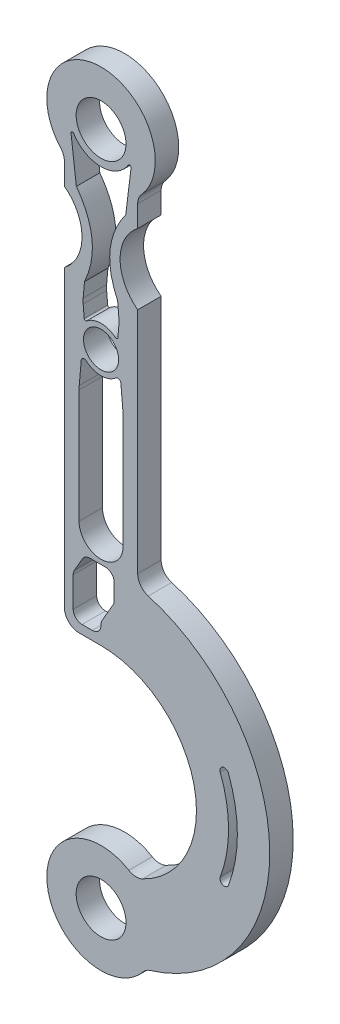
SolidWorks part; units mm, degrees
material "1.0577 (S355J2G4)"
ref_plane "Front Plane" through (0, 0, 0) normal (0, 0, 1) x (1, 0, 0)
ref_plane "Top Plane" through (0, 0, 0) normal (0, 1, 0) x (1, 0, 0)
ref_plane "Right Plane" through (0, 0, 0) normal (1, 0, 0) x (0, 0, -1)
sketch "Sketch1" plane through (0, 0, 0) normal (0, 0, 1) x (1, 0, 0)
  line L0 (-12.5, -13.6382) -> (-12.5, -23)
  line L1 (12.5, -13.6382) -> (12.5, -23)
  line L2 (0, 0) -> (0, -87.0636) construction
  line L3 (-12.5, -47) -> (-12.5, -154.9531)
  line L4 (12.5, -47) -> (12.5, -128.8307)
  line L5 (0, -152.4567) -> (-12.5, -152.4567)
  line L6 (15.2393, -240.4887) -> (11.4444, -215.4646) construction
  line L7 (0, -230) -> (17.3612, -226.5161)
  line L8 (-12.5, -13) -> (12.5, -13) construction
  line L9 (12.5, -57) -> (-12.5, -57) construction
  line L10 (15.3984, 118.8193) -> (165.3984, 118.8193) construction
  line L11 (-7.5, -119.4567) -> (-7.5, -80.6549)
  line L12 (6.7563, -71.4995) -> (7.4429, -79.3476)
  line L13 (-6.7563, -71.4995) -> (-7.4429, -79.3476)
  line L14 (7.5, -119.4567) -> (7.5, -80.6549)
  line L15 (-10.2431, -6.1641) -> (-8.4215, -21)
  line L16 (10.2431, -6.1641) -> (8.4215, -21)
  line L17 (-11, 0) -> (-10.6733, -2.6611) construction
  line L18 (11, 0) -> (10.6733, -2.6611) construction
  line L19 (0, -65) -> (24.057, -65) construction
  line L20 (6.5501, -60.8577) -> (7.4429, -50.6524) construction
  line L21 (-6.5501, -60.8577) -> (-7.4429, -50.6524) construction
  line L22 (-5.7376, -58.6709) -> (-6.0948, -54.5877)
  line L23 (-6.1711, -53.7161) -> (-17.293, -53.7161) construction
  line L24 (5.7376, -58.6709) -> (6.0948, -54.5877)
  line L25 (5.6481, -47.739) -> (6.0948, -52.8446)
  line L26 (-5.6481, -47.739) -> (-6.0948, -52.8446)
  line L27 (35.2514, 318.7905) -> (255.9181, 318.7905) construction
  line L28 (-9.5, -47) -> (-9.5, -154.9531) construction
  line L29 (0, -149.4567) -> (-12.5, -149.4567) construction
  line L30 (-3, -149.4567) -> (-6.5, -149.4567)
  line L31 (-9.5, -146.4567) -> (-9.5, -136.2605)
  line L32 (-9.0981, -134.7605) -> (-6.366, -130.0285)
  line L33 (-3.7679, -128.5285) -> (1.5, -128.5285)
  line L34 (4.5, -131.5285) -> (4.5, -136.8586)
  line L35 (4.0981, -138.3586) -> (0.4019, -144.7605)
  line L36 (0, -146.2605) -> (0, -146.4567)
  line L37 (-6.5, -35) -> (6.5, -35) construction
  line L38 (0, -185) -> (45, -185) construction
  circle A0 centre (0, 0) radius 8.5
  arc A1 (-12.5, -13.6382) -> (12.5, -13.6382) centre (0, 0) cw
  arc A2 (-12.5, -23) -> (-12.5, -47) centre (-21.5, -35) cw
  arc A3 (12.5, -23) -> (12.5, -47) centre (21.5, -35) ccw
  arc A4 (-12.5, -154.9531) -> (11.4444, -215.4646) centre (0, -185) cw
  arc A5 (11.4444, -215.4646) -> (15.2393, -240.4887) centre (0, -230) ccw
  arc A6 (15.2393, -240.4887) -> (12.5, -128.8307) centre (0, -185) ccw
  circle A7 centre (0, -230) radius 8.5
  arc A8 (0, -230) -> (0, -140) centre (0, -185) ccw construction
  circle A9 centre (0, -65) radius 6
  arc A10 (-5.1018, -70.8339) -> (5.1018, -70.8339) centre (0, -65) ccw
  arc A11 (-7.5, -119.4567) -> (7.5, -119.4567) centre (0, -119.4567) ccw
  arc A12 (7.5, -80.6549) -> (7.4429, -79.3476) centre (-7.5, -80.6549) ccw
  arc A13 (-7.5, -80.6549) -> (-7.4429, -79.3476) centre (7.5, -80.6549) cw
  arc A14 (-9.3231, -5.8378) -> (9.3231, -5.8378) centre (0, 0) ccw
  arc A16 (10.6733, -2.6611) -> (11, 0) centre (0, 0) ccw construction
  arc A17 (6.0948, -54.5877) -> (6.0948, -52.8446) centre (-3.8671, -53.7161) ccw
  arc A18 (-6.0948, -54.5877) -> (-6.0948, -52.8446) centre (3.8671, -53.7161) cw
  arc A20 (-6.5501, -60.8577) -> (-7.75, -65) centre (0, -65) ccw construction
  arc A21 (-7.75, -65) -> (-6.5501, -69.1423) centre (0, -65) ccw construction
  arc A22 (4.9219, -59.0136) -> (-4.9219, -59.0136) centre (0, -65) ccw
  arc A23 (6.5501, -69.1423) -> (7.75, -65) centre (0, -65) ccw construction
  arc A24 (7.75, -65) -> (6.5501, -60.8577) centre (0, -65) ccw construction
  arc A25 (-5.6481, -59.6933) -> (-6.5501, -60.8577) centre (0, -65) ccw construction
  arc A26 (6.5501, -60.8577) -> (5.6481, -59.6933) centre (0, -65) ccw construction
  arc A29 (-9.5, -136.2605) -> (-9.0981, -134.7605) centre (-6.5, -136.2605) cw
  arc A30 (-9.5, -146.4567) -> (-6.5, -149.4567) centre (-6.5, -146.4567) ccw
  arc A31 (0, -146.2605) -> (0.4019, -144.7605) centre (3, -146.2605) cw
  arc A32 (4.0981, -138.3586) -> (4.5, -136.8586) centre (1.5, -136.8586) ccw
  arc A33 (-6.366, -130.0285) -> (-3.7679, -128.5285) centre (-3.7679, -131.5285) cw
  arc A34 (4.5, -131.5285) -> (1.5, -128.5285) centre (1.5, -131.5285) ccw
  arc A35 (-3, -149.4567) -> (0, -146.4567) centre (-3, -146.4567) ccw
  arc A36 (6.7563, -71.4995) -> (5.1018, -70.8339) centre (5.7601, -71.5866) ccw
  arc A37 (-5.1018, -70.8339) -> (-6.7563, -71.4995) centre (-5.7601, -71.5866) ccw
  arc A38 (10.2431, -6.1641) -> (9.3231, -5.8378) centre (9.7469, -6.1032) ccw
  arc A39 (-10.2431, -6.1641) -> (-9.3231, -5.8378) centre (-9.7469, -6.1032) cw
  arc A40 (4.9219, -59.0136) -> (5.7376, -58.6709) centre (5.2395, -58.6274) ccw
  arc A41 (-4.9219, -59.0136) -> (-5.7376, -58.6709) centre (-5.2395, -58.6274) cw
  arc A42 (42.0595, -169) -> (42.0595, -201) centre (0, -185) cw construction
  arc A43 (43.4615, -201.5333) -> (43.4615, -168.4667) centre (0, -185) ccw
  arc A44 (40.6575, -200.4667) -> (40.6575, -169.5333) centre (0, -185) ccw
  arc A45 (40.6575, -200.4667) -> (43.4615, -201.5333) centre (42.0595, -201) ccw
  arc A46 (43.4615, -168.4667) -> (40.6575, -169.5333) centre (42.0595, -169) ccw
  spline S0 degree 2 poles (-5.6481, -47.739) (0.8771, -33.7172) (-8.4215, -21) knots 0 0 0 1 1 1
  spline S1 degree 2 poles (5.6481, -47.739) (-0.8771, -33.7172) (8.4215, -21) knots 0 0 0 1 1 1
  spline S2 degree 2 poles (42.0595, -169) (47.9405, -185) (42.0595, -201) knots 0 0 0 1 1 1
  point P11 (-6.5, -35)
  point P21 (13.3418, -227.9767)
  point P25 (6.5, -35)
  point P47 (7.5, -80)
  point P50 (-7.5, -80)
  point P57 (-3, -35)
  point P72 (6.1711, -53.7161)
  point P75 (-6.1711, -53.7161)
  point P80 (-8.4215, -21)
  point P83 (8.4215, -21)
  point P99 (-9.5, -135.4567)
  point P102 (-9.5, -149.4567)
  point P105 (0, -145.4567)
  point P110 (-5.5, -128.5285)
  point P132 (42.0595, -169)
  point P135 (42.0595, -201)
  point P138 (45, -185)
  dimension "D1" = 17
  dimension "D2" = 10
  dimension "D3" = 17
  dimension "D4" = 25
  dimension "D7" = 230
  dimension "D9" = 10
  dimension "D11" = 15
  dimension "D12" = 185
  dimension "D13" = 12
  dimension "D10" = 65
  dimension "D18" = 15.5
  dimension "D23" = 15
  dimension "D24" = 22
  dimension "D30" = 10
  dimension "D31" = 1
  dimension "D39" = 3
  dimension "D40" = 3
  dimension "D41" = 1
  dimension "D42" = 0.5
  dimension "D43" = 0.5
  dimension "D44" = 0.5
  dimension "D45" = 0.5
  dimension "D47" = 3
  dimension "D5" = 13
  dimension "D6" = 25
  dimension "D8" = 35
  dimension "D14" = 9
  dimension "D15" = 24
  dimension "D16" = 10
  dimension "D17" = 10
  dimension "D19" = 5
  dimension "D20" = 33
  dimension "D21" = 15
  dimension "D22" = 175
  dimension "D25" = 7
  dimension "D26" = 21
  dimension "D27" = 3
  dimension "D28" = 1
  dimension "D29" = 6
  dimension "D34" = 14
  dimension "D35" = 150
  dimension "D36" = 8
  dimension "D37" = 14
  dimension "D38" = 4
  dimension "D46" = 16
  dimension "D32" = 3
  dimension "D33" = 3
extrude "Boss-Extrude1" add sketch "Sketch1" along normal blind 8 contours A5 A6 L4 A3 L1 A1 L0 A2 L3 L5 A4 A7 A0
sketch "Sketch2" plane through (0, 0, 8) normal (0, 0, 1) x (1, 0, 0)
  line L0 (-12.5, -95) -> (-11, -92.4)
  line L1 (-12.5, -47) -> (-12.5, -152.4567) construction
  line L2 (-11, -92.4) -> (-11, -99.5)
  line L3 (-11, -99.5) -> (-10.5, -100)
  line L4 (-10.5, -100) -> (-4.1667, -100)
  line L7 (-10.5, -100) -> (-11, -100.5)
  line L8 (-11, -100.5) -> (-11, -107.6)
  line L9 (-11, -107.6) -> (-12.5, -105)
  dimension "D1" = 10
  dimension "D2" = 1.5
  dimension "D3" = 2
  dimension "D4" = 1
  dimension "D5" = 7.6
  dimension "D6" = 8.3333
  dimension "D7" = 100
extrude "Cut-Extrude1" [suppressed] cut sketch "Sketch2" against normal through all
fillet "Fillet1" radius 5 6 edges at (15.2393, -240.4887, 4) (11.4444, -215.4646, 4) (12.5, -13.6382, 4) (-12.5, -13.6382, 4) (12.5, -128.8307, 4) (-12.5, -152.4567, 4)
